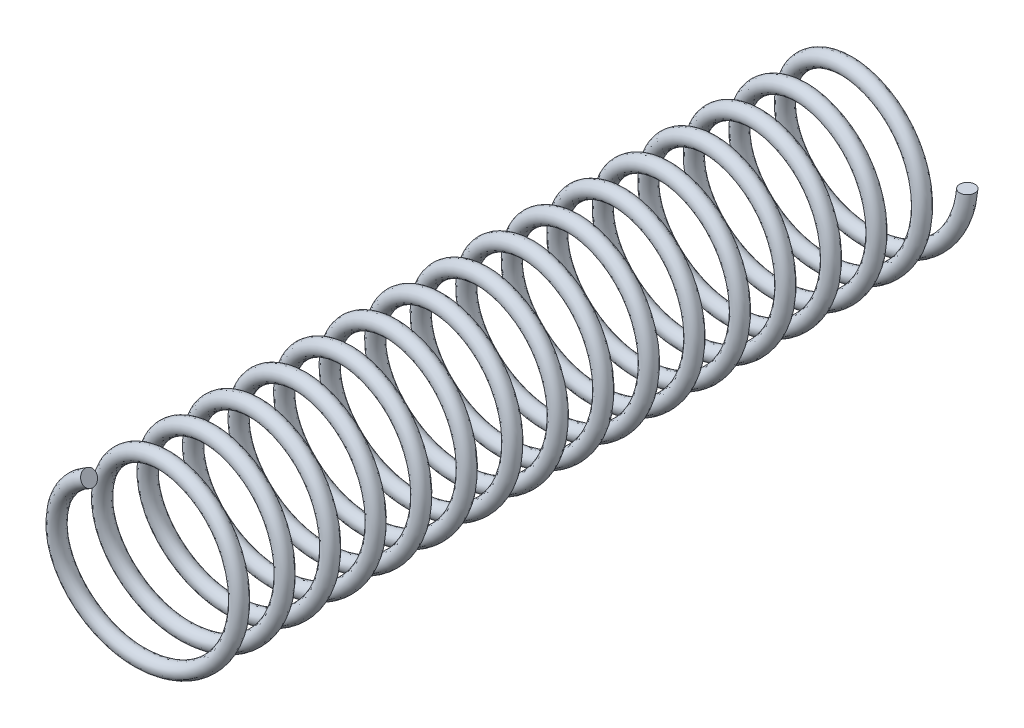
SolidWorks part; units mm, degrees
ref_plane "Plano frontal" through (0, 0, 0) normal (0, 0, 1) x (1, 0, 0)
ref_plane "Plano superior" through (0, 0, 0) normal (0, 1, 0) x (1, 0, 0)
ref_plane "Plano direito" through (0, 0, 0) normal (1, 0, 0) x (0, 0, -1)
sketch "Esboço1" plane through (0, 0, 0) normal (0, 0, 1) x (1, 0, 0)
  circle A0 centre (0, 0) radius 1.05
  dimension "D1" = 2.1
curve "Hélice/Espiral2" pitch 0.6 height 10 turns 16.6667
sketch "Esboço3" plane through (0, 0, 0) normal (1, 0, 0) x (0, 0, -1)
  circle A0 centre (-9.45, 1.0499) radius 0.1
  dimension "D1" = 0.2
sweep "Varredura3" add profiles "Esboço3" path "Hélice/Espiral2"
